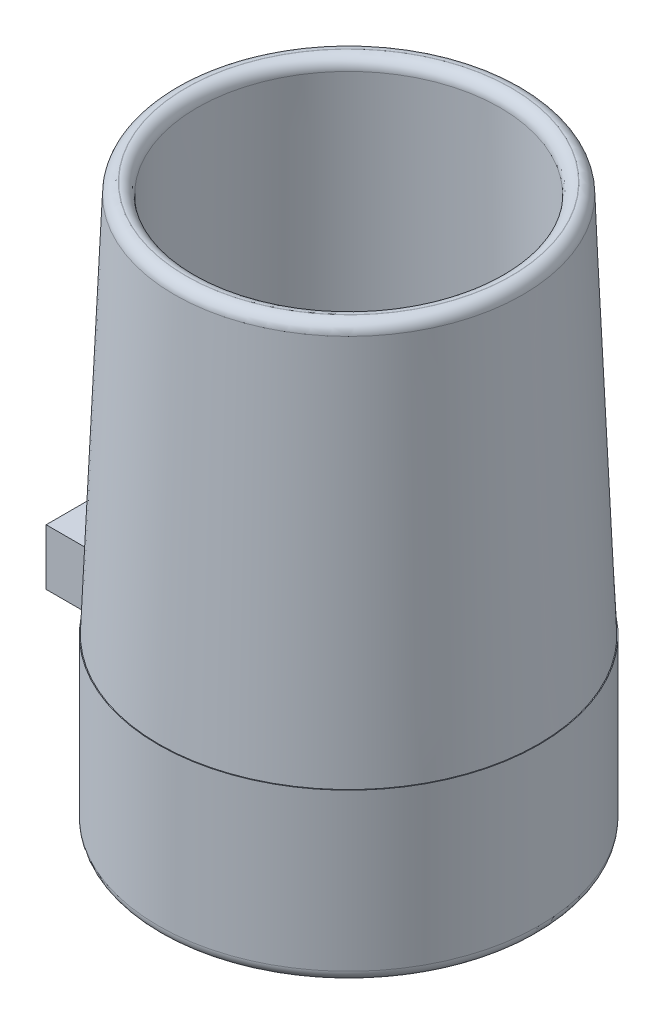
SolidWorks part; units mm, degrees
ref_plane "前视基准面" through (0, 0, 0) normal (0, 0, 1) x (1, 0, 0)
ref_plane "上视基准面" through (0, 0, 0) normal (0, 1, 0) x (1, 0, 0)
ref_plane "右视基准面" through (0, 0, 0) normal (1, 0, 0) x (0, 0, -1)
other "Configuration Table"
sketch "草图1" plane through (0, 0, 0) normal (0, 1, 0) x (1, 0, 0)
  circle A0 centre (0, 0) radius 17
  circle A1 centre (0, 0) radius 14
  dimension "D1" = 34
  dimension "D2" = 28
extrude "凸台-拉伸1" add sketch "草图1" along normal blind 15
sketch "草图2" plane through (0, 0, 0) normal (0, 1, 0) x (1, 0, 0)
  circle A0 centre (0, 0) radius 15.1
  circle A1 centre (0, 0) radius 14
  dimension "D2" = 30.2
  dimension "D1" = 28
extrude "切除-拉伸1" cut sketch "草图2" along normal blind 1.7
ref_plane "基准面1" through (0, 15, 0) normal (0, 1, 0) x (1, 0, 0)
sketch "草图3" plane through (0, 15, 0) normal (0, 1, 0) x (1, 0, 0)
  line L0 (-22, 5) -> (-22, -5)
  line L1 (-22, -5) -> (-16.2481, -5)
  line L2 (-22, 5) -> (-16.2481, 5)
  circle A0 centre (0, 0) radius 17 construction
  arc A1 (-16.2481, 5) -> (-16.2481, -5) centre (0, 0) ccw
  point P5 (-22, 0)
  dimension "D2" = 10
  dimension "D1" = 22
extrude "凸台-拉伸2" add sketch "草图3" against normal blind 5
ref_plane "基准面2" through (0, 50, 0) normal (0, 1, 0) x (1, 0, 0)
sketch "草图4" plane through (0, 50, 0) normal (0, 1, 0) x (1, 0, 0)
  circle A0 centre (0, 0) radius 13.5
  circle A1 centre (0, 0) radius 15.5
  dimension "D1" = 27
  dimension "D2" = 31
sketch "草图5" plane through (0, 0, 0) normal (0, 0, 1) x (1, 0, 0)
  line L0 (0, 50) -> (0, 28.7627) construction
sketch "草图9" plane through (0, 50, 0) normal (0, 1, 0) x (1, 0, 0)
  line L0 (0, 0) -> (13.5, 0)
  line L1 (13.5, 0) -> (15.5, 0)
  circle A0 centre (0, 0) radius 13.5 construction
  circle A1 centre (0, 0) radius 15.5 construction
sketch "草图10" plane through (0, 15, 0) normal (0, 1, 0) x (1, 0, 0)
  line L0 (0, 0) -> (14, 0)
  line L1 (13.5, 0) -> (15.5, 0) construction
  line L2 (14, 0) -> (16.9337, 0)
  circle A0 centre (0, 0) radius 14 construction
sketch "草图11" plane through (0, 0, 0) normal (0, 0, 1) x (1, 0, 0)
  line L0 (13.5, 50) -> (14, 15)
  line L1 (15.5, 50) -> (-15.5, 50) construction
  line L2 (13.5, 50) -> (-13.5, 50) construction
  line L3 (0, 15) -> (14, 15) construction
  line L4 (14, 15) -> (16.9337, 15) construction
  line L5 (14, 15) -> (16.9337, 15)
  line L6 (18.7, 15) -> (-18.7, 15) construction
  line L7 (16.9337, 15) -> (15.5, 50)
  line L8 (13.5, 50) -> (15.5, 50) construction
  line L9 (15.5, 50) -> (13.5, 50)
revolve "旋转1" add sketch "草图11" angle 360 about L0
fillet "圆角1" radius 1 3 edges at (0, 0, 17) (0, 50, 15.5) (0, 50, 13.5)
fillet "圆角2" radius 1 2 edges at (-16.2481, 12.5, 5) (-16.2481, 12.5, -5)
